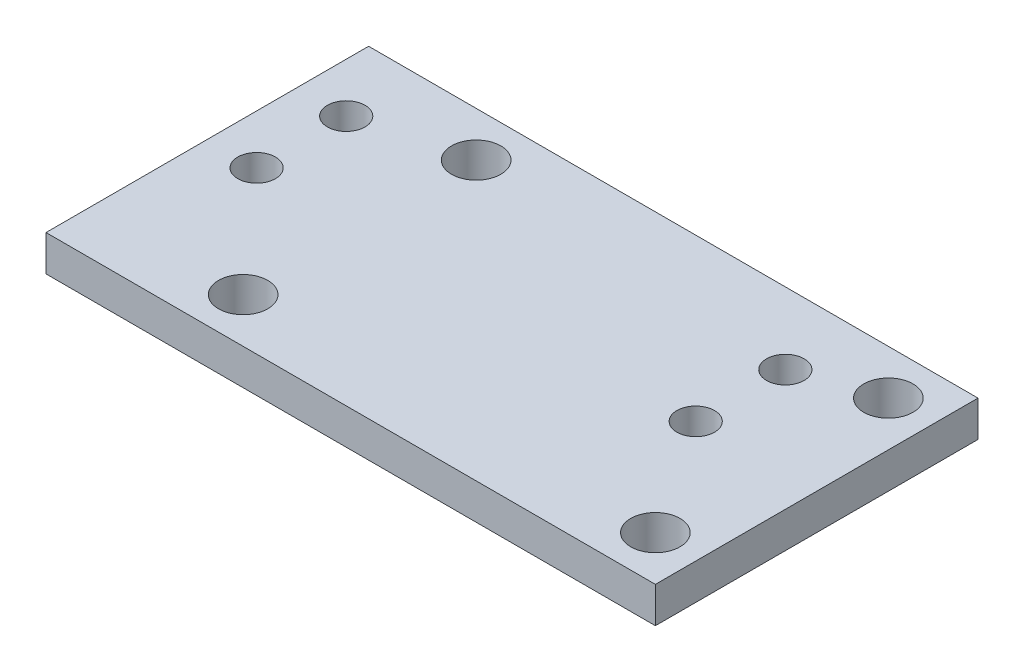
SolidWorks part; units mm, degrees
ref_plane "前视基准面" through (0, 0, 0) normal (0, 0, 1) x (1, 0, 0)
ref_plane "上视基准面" through (0, 0, 0) normal (0, 1, 0) x (1, 0, 0)
ref_plane "右视基准面" through (0, 0, 0) normal (1, 0, 0) x (0, 0, -1)
sketch "草图1" plane through (0, 0, 0) normal (0, 1, 0) x (1, 0, 0)
  line L0 (-29.9191, 27.4812) -> (16.0809, 27.4812) construction
  line L1 (-29.9191, 1.4812) -> (-29.9191, 27.4812) construction
  line L2 (-29.9191, 1.4812) -> (16.0809, 1.4812) construction
  line L3 (16.0809, 1.4812) -> (16.0809, 27.4812) construction
  line L4 (-6.9191, 27.4812) -> (-6.9191, 1.4812) construction
  line L5 (-29.9191, 14.4812) -> (16.0809, 14.4812) construction
  line L6 (-34.9191, 32.4812) -> (21.0809, 32.4812)
  line L8 (-29.9191, 14.4812) -> (-51.9173, 14.4812) construction
  line L9 (-6.9191, 27.4812) -> (-6.9191, 42.3041) construction
  line L10 (-34.9191, -3.5188) -> (21.0809, -3.5188)
  line L11 (21.0809, 32.4812) -> (21.0809, -3.5188)
  line L12 (-34.9191, 32.4812) -> (-46.9191, 32.4812)
  line L13 (-46.9191, 32.4812) -> (-46.9191, -3.5188)
  line L14 (-46.9191, -3.5188) -> (-34.9191, -3.5188)
  circle A0 centre (-29.9191, 27.4812) radius 2.75
  circle A1 centre (16.0809, 27.4812) radius 2.75
  circle A2 centre (-29.9191, 1.4812) radius 2.75
  circle A3 centre (16.0809, 1.4812) radius 2.75
  circle A4 centre (7.5809, 14.4812) radius 2.1
  circle A5 centre (7.5809, 24.4812) radius 2.1
  circle A6 centre (-41.4191, 24.4812) radius 2.1
  circle A7 centre (-41.4191, 14.4812) radius 2.1
  point P18 (-34.9191, 14.4812)
  point P20 (-6.9191, -3.5188)
  point P21 (-6.9191, 32.4812)
  dimension "D1" = 5.5
  dimension "D2" = 5.5
  dimension "D4" = 40
  dimension "D7" = 14.5
  dimension "D8" = 49
  dimension "D3" = 46
  dimension "D5" = 18
  dimension "D6" = 26
  dimension "D9" = 10
  dimension "D10" = 18
  dimension "D11" = 49
extrude "凸台-拉伸1" add sketch "草图1" along normal blind 4
